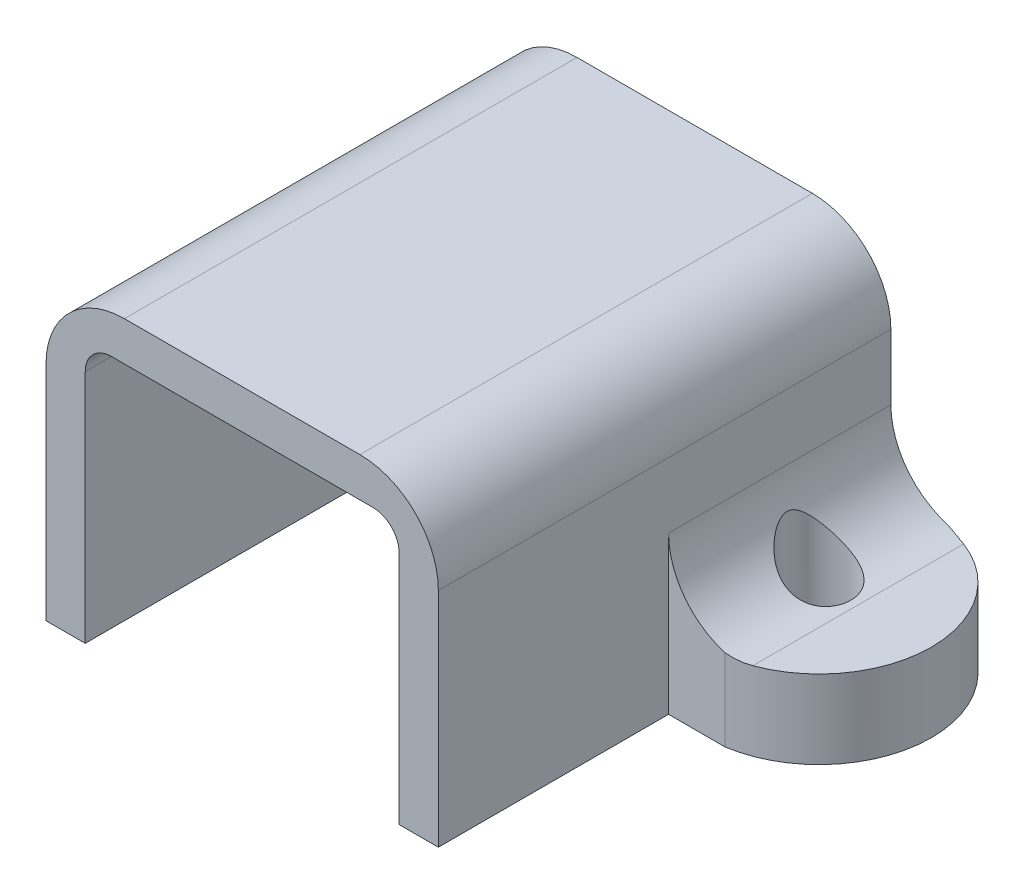
SolidWorks part; units mm, degrees
material "ABS"
ref_plane "Front Plane" through (0, 0, 0) normal (0, 0, 1) x (1, 0, 0)
ref_plane "Top Plane" through (0, 0, 0) normal (0, 1, 0) x (1, 0, 0)
ref_plane "Right Plane" through (0, 0, 0) normal (1, 0, 0) x (0, 0, -1)
sketch "Sketch1" plane through (0, 0, 0) normal (0, 0, 1) x (1, 0, 0)
  line L0 (-13.3, 0) -> (-6, 0)
  line L1 (-13.3, 0) -> (-13.3, 3)
  line L2 (-13.3, 3) -> (-10.5, 3)
  line L3 (-7.5, 6) -> (-7.5, 8.5)
  line L4 (-4.5, 11.5) -> (4.5, 11.5)
  line L5 (0, 11.5) -> (0, 0) construction
  line L6 (7.5, 6) -> (7.5, 8.5)
  line L7 (13.3, 3) -> (10.5, 3)
  line L8 (13.3, 0) -> (13.3, 3)
  line L9 (-6, 0) -> (-6, 9)
  line L10 (-5, 10) -> (5, 10)
  line L11 (6, 0) -> (6, 9)
  line L12 (6, 0) -> (13.3, 0)
  arc A0 (7.5, 8.5) -> (4.5, 11.5) centre (4.5, 8.5) ccw
  arc A1 (-7.5, 8.5) -> (-4.5, 11.5) centre (-4.5, 8.5) cw
  arc A2 (-10.5, 3) -> (-7.5, 6) centre (-10.5, 6) ccw
  arc A3 (7.5, 6) -> (10.5, 3) centre (10.5, 6) ccw
  arc A4 (-6, 9) -> (-5, 10) centre (-5, 9) cw
  arc A5 (6, 9) -> (5, 10) centre (5, 9) ccw
  point P13 (7.5, 11.5)
  point P16 (-7.5, 11.5)
  point P19 (-7.5, 3)
  point P22 (7.5, 3)
  point P31 (0, 10)
  dimension "D5" = 3
  dimension "D8" = 1
  dimension "D1" = 26.6
  dimension "D2" = 15
  dimension "D3" = 11.5
  dimension "D4" = 3
  dimension "D6" = 12
  dimension "D7" = 1.5
extrude "Extrude1" add sketch "Sketch1" along normal blind 17.3
sketch "Sketch2" plane through (0, 0, 17.3) normal (0, 0, 1) x (1, 0, 0)
  line L1 (-13.3, 0) -> (-6, 0) construction
  line L2 (-13.3, 0) -> (-7.5, 0)
  line L3 (-13.3, 0) -> (-13.3, 8.5)
  line L4 (-13.3, 8.5) -> (-7.5, 8.5)
  line L6 (-7.5, 0) -> (-7.5, 8.5)
  line L7 (-13.3, 3) -> (-13.3, 0) construction
  line L9 (13.3, 0) -> (7.5, 0)
  line L10 (13.3, 0) -> (13.3, 8.5)
  line L11 (13.3, 8.5) -> (7.5, 8.5)
  line L12 (7.5, 0) -> (7.5, 8.5)
extrude "Extrude2" cut sketch "Sketch2" against normal blind 8.8
sketch "Sketch3" plane through (0, 0, 0) normal (0, -1, 0) x (1, 0, 0)
  line L2 (7.5, 8.5) -> (13.3, 8.5) construction
  line L3 (6, 0) -> (13.3, 0) construction
  line L4 (13.3, 8.5) -> (13.3, 0) construction
  line L5 (9.6538, 8.5) -> (9.6538, 9.263)
  line L6 (9.6538, 9.263) -> (15.0793, 9.263)
  line L7 (15.0793, 9.263) -> (15.0793, -0.4862)
  line L8 (15.0793, -0.4862) -> (9.6538, -0.4862)
  line L9 (9.6538, -0.4862) -> (9.6538, 0)
  line L10 (0, 17.3) -> (0, 0) construction
  line L11 (-5, 17.3) -> (5, 17.3) construction
  line L12 (-9.6538, -0.4862) -> (-9.6538, 0)
  line L13 (-15.0793, -0.4862) -> (-9.6538, -0.4862)
  line L14 (-15.0793, 9.263) -> (-15.0793, -0.4862)
  line L15 (-9.6538, 9.263) -> (-15.0793, 9.263)
  line L16 (-9.6538, 8.5) -> (-9.6538, 9.263)
  arc A0 (9.6538, 8.5) -> (9.6538, 0) centre (9, 4.25) cw
  arc A1 (-9.6538, 8.5) -> (-9.6538, 0) centre (-9, 4.25) ccw
  circle A2 centre (-9, 4.25) radius 1
  circle A3 centre (9, 4.25) radius 1
  dimension "D1" = 2
  dimension "D2" = 18
extrude "Extrude3" cut sketch "Sketch3" against normal blind 5
hole_wizard "#2 Clearance Hole1" positions "3DSketch1" profile "Sketch4" hole size "#2" standard "Ansi Inch" end condition up to next
sketch3d "3DSketch1"
  line L0 (-9, 3.5214, 4.25) -> (-9, 0, 4.25) construction
  line L1 (9, 3.5201, 4.25) -> (9, 0, 4.25) construction
  point P0 (-9, 0, 4.25)
  point P2 (9, 0, 4.25)
sketch "Sketch4" plane through (-9, 0, 4.25) normal (1, 0, 0) x (0, 0, -1)
  line L0 (0, 0) -> (0, 11.5)
  line L1 (0, 11.5) -> (1.2192, 11.5)
  line L2 (1.2192, 11.5) -> (1.2192, 0)
  line L5 (1.2192, 0) -> (0, 0)
  line L11 (0, -6.35) -> (0, 107.95) construction
  dimension "Thru Hole Dia." = 2.4384
  dimension "Thru Hole Depth" = 11.5
